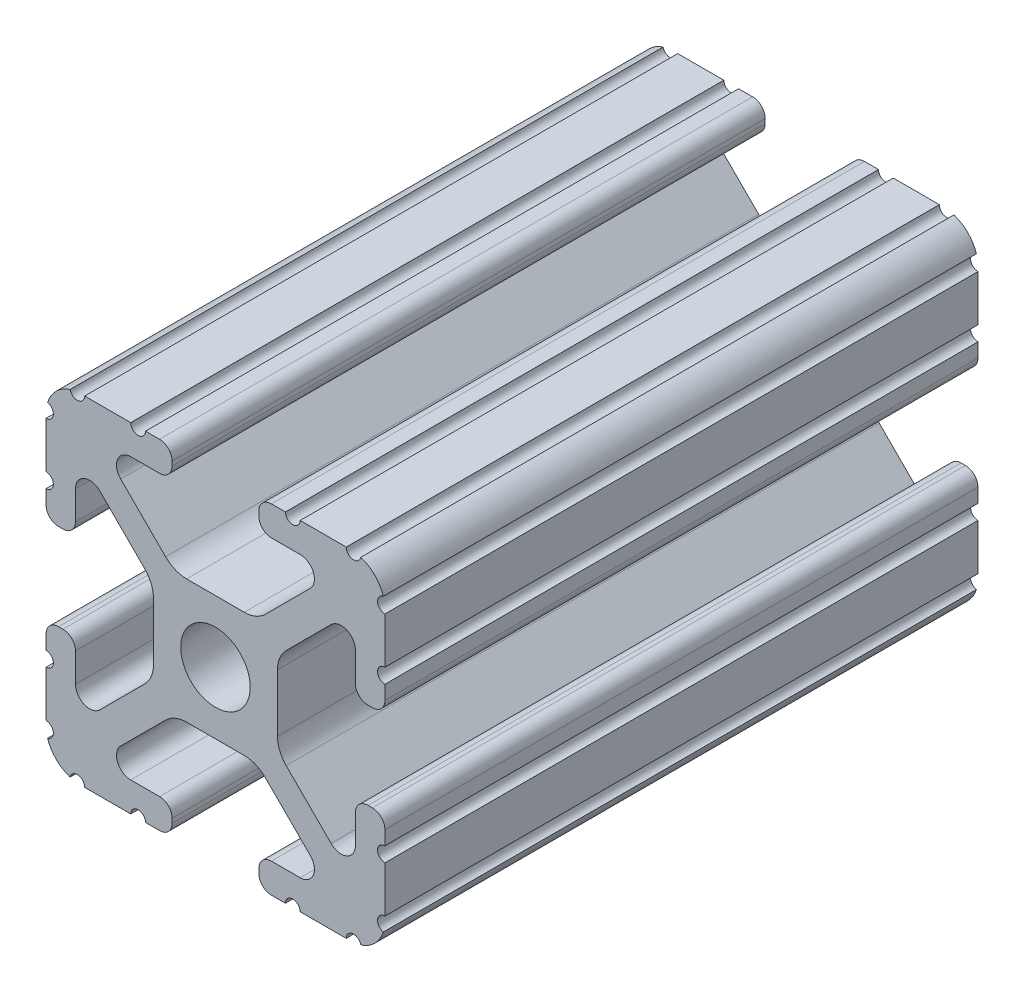
SolidWorks part; units mm, degrees
ref_plane "Front Plane" through (0, 0, 0) normal (0, 0, 1) x (1, 0, 0)
ref_plane "Top Plane" through (0, 0, 0) normal (0, 1, 0) x (1, 0, 0)
ref_plane "Right Plane" through (0, 0, 0) normal (1, 0, 0) x (0, 0, -1)
sketch "Sketch2" plane through (0, 0, 0) normal (0, 0, 1) x (1, 0, 0)
  line L0 (0, 12.7) -> (0, -12.7) construction
  line L1 (-12.7, 0) -> (12.7, 0) construction
  line L2 (3.2512, -12.7) -> (12.7, -12.7)
  line L3 (12.7, -12.7) -> (12.7, -3.2512)
  line L4 (3.2512, -12.7) -> (3.2512, -10.4902)
  line L5 (3.2512, -10.4902) -> (8.9276, -10.4902)
  line L6 (8.9276, -10.4902) -> (3.0856, -4.6482)
  line L7 (0, 0) -> (12.7, -12.7) construction
  line L8 (12.7, -3.2512) -> (10.4902, -3.2512)
  line L9 (10.4902, -3.2512) -> (10.4902, -8.9276)
  line L10 (10.4902, -8.9276) -> (4.6482, -3.0856)
  circle A0 centre (0, 0) radius 2.6035
  arc A1 (6.3485, -10.4902) -> (7.1039, -8.6665) centre (6.3485, -9.4219) ccw construction
  point P8 (0, -4.6482)
  dimension "Center Hole Diameter" = 5.207
  dimension "Rail Height" = 25.4
  dimension "Rail Width" = 25.4
  dimension "T-Slot Width" = 6.5024
  dimension "Slot Inner Width" = 14.8336
  dimension "Thickness" = 2.2098
  dimension "Slot Depth" = 5.842
  dimension "D1" = 2.2098
sketch "Sketch3" plane through (0, 0, 0) normal (1, 0, 0) x (0, 0, -1)
  line L0 (-76.2, -12.7) -> (76.2, -12.7) construction
  line L1 (-68.58, 0) -> (68.58, 0) construction
  dimension "Length" = 152.4
  dimension "D1" = 137.16
sketch "Sketch4" plane through (0, 0, 0) normal (0, 0, 1) x (1, 0, 0)
  line L0 (4.1904, -12.7) -> (10.1173, -12.7)
  line L1 (3.2512, -12.7) -> (12.7, -12.7) construction
  line L2 (3.2512, -12.7) -> (3.2512, -10.4902) construction
  line L3 (3.2512, -10.4902) -> (8.9276, -10.4902) construction
  line L4 (3.2512, -11.4294) -> (3.2512, -11.7608)
  line L5 (4.1904, -10.4902) -> (6.3485, -10.4902)
  line L6 (0, -4.6482) -> (2.164, -4.6482)
  line L7 (8.9276, -10.4902) -> (3.0856, -4.6482) construction
  line L8 (3.7373, -5.2999) -> (7.1039, -8.6665)
  line L9 (12.7, -12.7) -> (12.7, -3.2512) construction
  line L10 (10.4902, -8.9276) -> (4.6482, -3.0856) construction
  line L11 (10.4902, -3.2512) -> (10.4902, -8.9276) construction
  line L12 (10.4902, -6.3485) -> (10.4902, -4.1904)
  line L13 (12.7, -3.2512) -> (10.4902, -3.2512) construction
  line L14 (11.4294, -3.2512) -> (11.7608, -3.2512)
  line L15 (12.7, -4.1904) -> (12.7, -10.1173)
  line L16 (8.6665, -7.1039) -> (5.2999, -3.7373)
  line L17 (4.6482, 0) -> (4.6482, -2.164)
  line L18 (-12.7, 0) -> (12.7, 0) construction
  line L19 (0, -4.6482) -> (0, -2.6035)
  line L20 (0, 12.7) -> (0, -12.7) construction
  line L21 (4.6482, 0) -> (2.6035, 0)
  arc A0 (3.2512, -11.7608) -> (4.1904, -12.7) centre (4.1904, -11.7608) ccw
  arc A2 (3.2512, -11.4294) -> (4.1904, -10.4902) centre (4.1904, -11.4294) cw
  arc A3 (6.3485, -10.4902) -> (7.1039, -8.6665) centre (6.3485, -9.4219) ccw
  arc A4 (2.164, -4.6482) -> (3.7373, -5.2999) centre (2.164, -6.8732) cw
  arc A5 (10.1173, -12.7) -> (12.7, -10.1173) centre (10.1173, -10.1173) ccw
  arc A6 (8.6665, -7.1039) -> (10.4902, -6.3485) centre (9.4219, -6.3485) ccw
  arc A7 (10.4902, -4.1904) -> (11.4294, -3.2512) centre (11.4294, -4.1904) cw
  arc A8 (11.7608, -3.2512) -> (12.7, -4.1904) centre (11.7608, -4.1904) cw
  arc A9 (5.2999, -3.7373) -> (4.6482, -2.164) centre (6.8732, -2.164) cw
  circle A10 centre (0, 0) radius 2.6035 construction
  arc A11 (0, -2.6035) -> (2.6035, 0) centre (0, 0) ccw
  dimension "D1" = 2.5827
  dimension "D2" = 2.225
  dimension "D3" = 0.9392
extrude "Boss-Extrude1" add sketch "Sketch4" along normal mid plane 44.45
sketch "Sketch5" plane through (0, 0, 0) normal (0, 0, 1) x (1, 0, 0)
  line L0 (3.2512, -12.7) -> (12.7, -12.7) construction
  line L1 (4.1904, -10.4902) -> (6.3485, -10.4902) construction
  line L3 (0, 0) -> (12.7, -12.7) construction
  line L4 (6.3485, -10.4902) -> (6.3485, -12.7) construction
  line L5 (8.9276, -10.4902) -> (3.0856, -4.6482) construction
  circle A0 centre (10.3562, -12.7) radius 0.5524
  circle A1 centre (5.796, -12.7) radius 0.5524
  circle A2 centre (12.7, -10.3562) radius 0.5524
  circle A3 centre (12.7, -5.796) radius 0.5524
  point P10 (5.2694, -10.4902)
  point P12 (9.4219, -6.3485)
  dimension "D1" = 1.1049
extrude "Cut-Extrude1" cut sketch "Sketch5" against normal through all both and the other way through all
mirror "Mirror1" about plane through (0, 0, 0) normal (1, 0, 0) of bodies 137 134
mirror "Mirror2" about plane through (0, 0, 0) normal (0, 1, 0) of bodies 135
sketch "Sketch6" plane through (0, 0, 0) normal (0, 1, 0) x (1, 0, 0)
  line L0 (0, 22.225) -> (0, 9.525) construction
  line L1 (0, -22.225) -> (0, -9.525) construction
  line L4 (2.164, 22.225) -> (-2.164, 22.225)
  line L5 (-2.164, 22.225) -> (-2.164, -22.225)
  line L6 (-2.164, -22.225) -> (2.164, -22.225)
  line L7 (2.164, -22.225) -> (2.164, 22.225)
  line L8 (2.164, 22.225) -> (-2.164, 22.225) construction
  line L9 (-2.164, 22.225) -> (-2.164, -22.225) construction
  line L10 (-2.164, -22.225) -> (2.164, -22.225) construction
  line L11 (2.164, -22.225) -> (2.164, 22.225) construction
  circle A0 centre (0, -9.525) radius 2.555
  circle A1 centre (0, 9.525) radius 2.555
  dimension "D2" = 12.7
  dimension "D3" = 5.11
  dimension "D1" = 0
extrude "Cut-Extrude2" cut sketch "Sketch6" against normal through all both and the other way through all
sketch "Sketch7" plane through (0, 0, 0) normal (1, 0, 0) x (0, 0, -1)
  line L0 (-22.225, 0) -> (3.175, 0) construction
  line L1 (-22.225, -2.164) -> (22.225, -2.164) construction
  line L6 (-22.225, -2.164) -> (-22.225, 2.164) construction
  line L7 (-22.225, 2.164) -> (22.225, 2.164) construction
  line L8 (22.225, -2.164) -> (22.225, 2.164) construction
  line L9 (-22.225, -2.164) -> (22.225, 2.164) construction
  line L10 (-22.225, 2.164) -> (22.225, -2.164) construction
  line L11 (22.225, 0) -> (-3.175, 0) construction
  circle A2 centre (-3.175, 0) radius 2.54
  circle A3 centre (3.175, 0) radius 2.54
  point P0 (0, 0)
  dimension "D1" = 25.4
  dimension "D2" = 5.08
extrude "Cut-Extrude3" cut sketch "Sketch7" against normal through all both and the other way through all
equation "\"D1@Boss-Extrude1\"=1.75in"
equation "\"D1@Sketch2\"=\"Thickness@Sketch2\""
equation "\"D2@Sketch4\"=\"Slot Inner Width@Sketch2\"*0.15"
equation "\"D1@Sketch4\"=\"D3@Sketch4\"*2.75"
equation "\"D3@Sketch4\"=\"Thickness@Sketch2\"*0.425"
equation "\"D1@Sketch5\"=\"Thickness@Sketch2\"*0.5"
equation "\"D1@Sketch3\"=\"Length@Sketch3\"*0.9"
